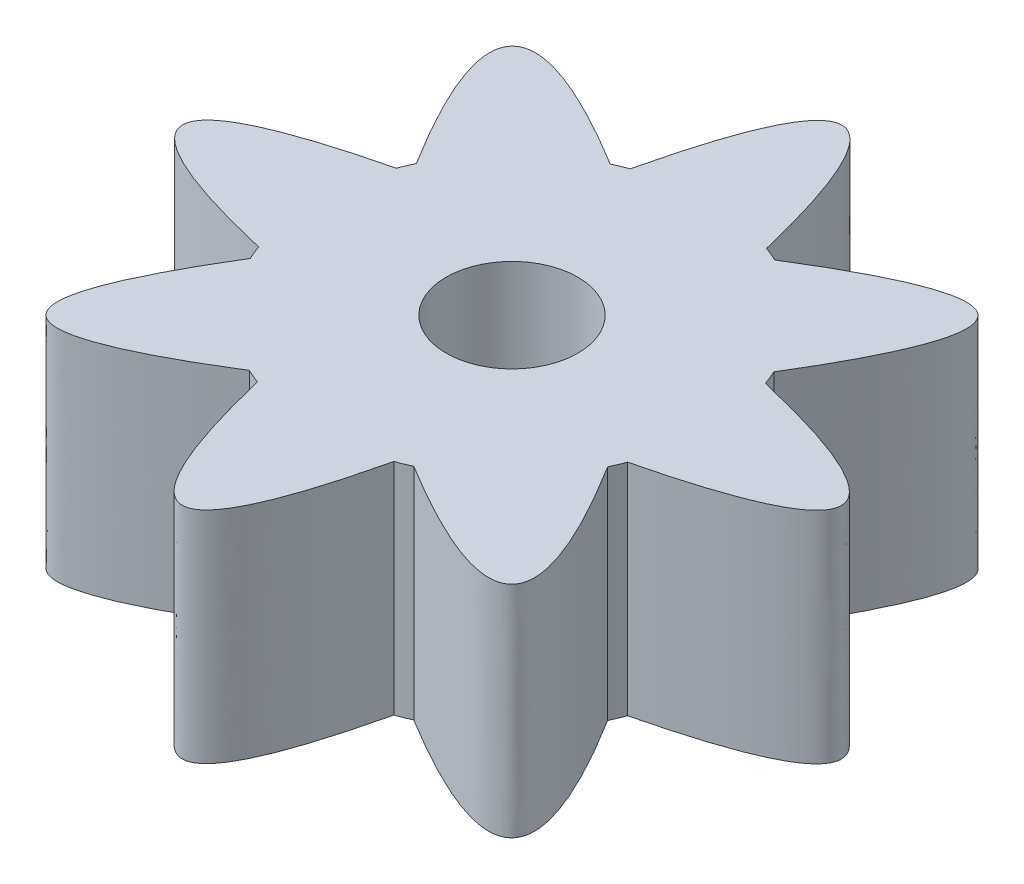
SolidWorks part; units mm, degrees
ref_plane "Front Plane" through (0, 0, 0) normal (0, 0, 1) x (1, 0, 0)
ref_plane "Top Plane" through (0, 0, 0) normal (0, 1, 0) x (1, 0, 0)
ref_plane "Right Plane" through (0, 0, 0) normal (1, 0, 0) x (0, 0, -1)
sketch "Sketch3" plane through (0, 0, 0) normal (0, 1, 0) x (1, 0, 0)
  line L1 (-6.002, -35) -> (-6, -38) construction
  circle A1 centre (-6, -42.5) radius 4.5
  dimension "D1" = 9
  dimension "D2" = 42.5
  dimension "D3" = 6
extrude "Boss-Extrude2" add sketch "Sketch3" along normal mid plane 5 contours A1
sketch "Sketch5" plane through (0, -2.5, 0) normal (0, -1, 0) x (1, 0, 0)
  line L0 (-7.5809, 46.7132) -> (-4.4606, 46.7285)
  circle A0 centre (-6, 42.5) radius 4.5 construction
  spline S0 degree 2 poles (-7.5809, 46.7132) (-5.9929, 53.2792) (-4.4606, 46.7285) knots 0 0 0 1 1 1
  dimension "D1" = 7.5
  dimension "D2" = 3.1204
extrude "Boss-Extrude3" add sketch "Sketch5" against normal through all
pattern_circular "CirPattern1" count 8 over 360 about axis through (-6, -2.5, 42.5) along (0, 1, 0) of "Boss-Extrude3"
sketch "Sketch7" plane through (0, -2.5, 0) normal (0, -1, 0) x (1, 0, 0)
  circle A0 centre (-6, 42.5) radius 1.5
extrude "Cut-Extrude1" cut sketch "Sketch7" against normal blind 5
